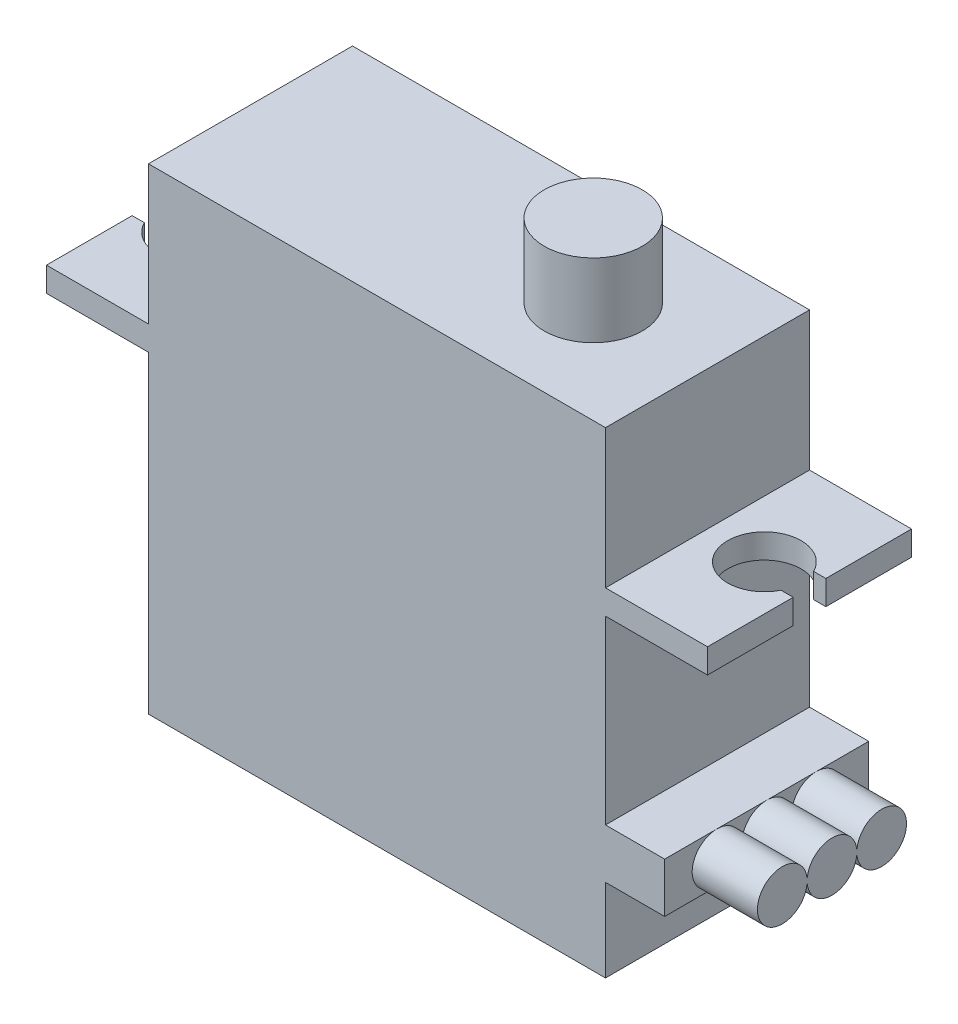
SolidWorks part; units mm, degrees
ref_plane "Front Plane" through (0, 0, 0) normal (0, 0, 1) x (1, 0, 0)
ref_plane "Top Plane" through (0, 0, 0) normal (0, 1, 0) x (1, 0, 0)
ref_plane "Right Plane" through (0, 0, 0) normal (1, 0, 0) x (0, 0, -1)
sketch "Sketch1" plane through (0, 0, 0) normal (0, 1, 0) x (1, 0, 0)
  line L0 (20.25, 0) -> (18.622, 0) construction
  line L1 (20.25, -6.25) -> (-20.25, -6.25)
  line L2 (20.25, -6.25) -> (20.25, -1)
  line L3 (20.25, 6.25) -> (-20.25, 6.25)
  line L4 (-20.25, -6.25) -> (-20.25, -1)
  line L5 (20.25, -6.25) -> (-20.25, 6.25) construction
  line L6 (20.25, 6.25) -> (-20.25, -6.25) construction
  line L7 (19.5, 1) -> (20.25, 1)
  line L8 (19.5, -1) -> (20.25, -1)
  line L10 (15.2344, 0) -> (-20.25, 0) construction
  line L11 (0, 0) -> (0, 14.0725) construction
  line L12 (-19.5, 1) -> (-20.25, 1)
  line L14 (-19.5, -1) -> (-20.25, -1)
  line L15 (20.25, 1) -> (20.25, 6.25)
  line L16 (-21.7988, 0) -> (-24.8476, 0) construction
  line L17 (-20.25, 1) -> (-20.25, 6.25)
  arc A0 (19.5, 1) -> (19.5, -1) centre (17.4844, 0) ccw
  arc A1 (-19.5, 1) -> (-19.5, -1) centre (-17.4844, 0) cw
  point P0 (0, 0)
  dimension "D3" = 4.5
  dimension "D1" = 12.5
  dimension "D2" = 40.5
  dimension "D5" = 0.75
extrude "Boss-Extrude1" add sketch "Sketch1" along normal blind 1.5
sketch "Sketch2" plane through (0, 1.5, 0) normal (0, 1, 0) x (1, 0, 0)
  line L0 (20.25, 6.25) -> (-20.25, 6.25) construction
  line L1 (14, -6.25) -> (-14, -6.25)
  line L2 (14, -6.25) -> (14, 6.25)
  line L3 (14, 6.25) -> (-14, 6.25)
  line L4 (-14, -6.25) -> (-14, 6.25)
  line L5 (14, -6.25) -> (-14, 6.25) construction
  line L6 (14, 6.25) -> (-14, -6.25) construction
  point P0 (0, 0)
  point P8 (0, 0)
  point P9 (0, 0)
  dimension "D1" = 28
extrude "Boss-Extrude2" add sketch "Sketch2" along normal blind 8.5
sketch "Sketch3" plane through (0, 10, 0) normal (0, 1, 0) x (1, 0, 0)
  line L0 (14, 0) -> (7, 0) construction
  line L1 (14, -6.25) -> (14, 6.25) construction
  circle A0 centre (7, 0) radius 3
  dimension "D1" = 6
  dimension "D2" = 7
extrude "Boss-Extrude3" add sketch "Sketch3" along normal blind 4.5
sketch "Sketch4" plane through (0, 0, 0) normal (0, -1, 0) x (1, 0, 0)
  line L0 (-20.25, 6.25) -> (20.25, 6.25) construction
  line L1 (14, -6.25) -> (-14, -6.25)
  line L2 (14, -6.25) -> (14, 6.25)
  line L3 (14, 6.25) -> (-14, 6.25)
  line L4 (-14, -6.25) -> (-14, 6.25)
  line L5 (14, -6.25) -> (-14, 6.25) construction
  line L6 (14, 6.25) -> (-14, -6.25) construction
  point P0 (0, 0)
  dimension "D1" = 28
extrude "Boss-Extrude4" add sketch "Sketch4" along normal blind 19.2
sketch "Sketch5" plane through (0, 0, 6.25) normal (0, 0, 1) x (1, 0, 0)
  line L0 (14, -19.2) -> (14, 0) construction
  line L1 (14, -11.0793) -> (17.625, -11.0793)
  line L2 (14, -11.0793) -> (14, -14.1238)
  line L3 (14, -14.1238) -> (17.625, -14.1238)
  line L4 (17.625, -11.0793) -> (17.625, -14.1238)
extrude "Boss-Extrude5" add sketch "Sketch5" against normal up to surface (12.5 mm away) up to face at (0, -1.0333, -6.25)
sketch "Sketch6" plane through (17.625, 0, 0) normal (1, 0, 0) x (0, 0, -1)
  line L0 (-6.25, -12.6015) -> (-4.5668, -12.6015) construction
  line L1 (-6.25, -14.1238) -> (-6.25, -11.0793) construction
  line L2 (6.25, -11.0793) -> (6.25, -14.1238) construction
  line L3 (0, -12.6015) -> (0, -8.0347) construction
  line L5 (-1.5325, -12.7778) -> (-1.512, -12.7778)
  line L7 (-1.5325, -12.4252) -> (-1.512, -12.4252)
  line L13 (2.4418, -12.6015) -> (6.25, -12.6015) construction
  line L14 (1.512, -12.4252) -> (1.5325, -12.4252)
  line L15 (1.512, -12.7778) -> (1.5325, -12.7778)
  arc A0 (-1.512, -12.7778) -> (1.512, -12.7778) centre (0, -12.6015) ccw
  arc A1 (1.5325, -12.7778) -> (1.5325, -12.4252) centre (3.0445, -12.6015) ccw
  arc A2 (-1.5325, -12.7778) -> (-1.5325, -12.4252) centre (-3.0445, -12.6015) cw
  arc A4 (1.512, -12.4252) -> (-1.512, -12.4252) centre (0, -12.6015) ccw
extrude "Boss-Extrude7" add sketch "Sketch6" along normal blind 4 contours L14 A1 L15 A0 L5 A2 L7 A4
